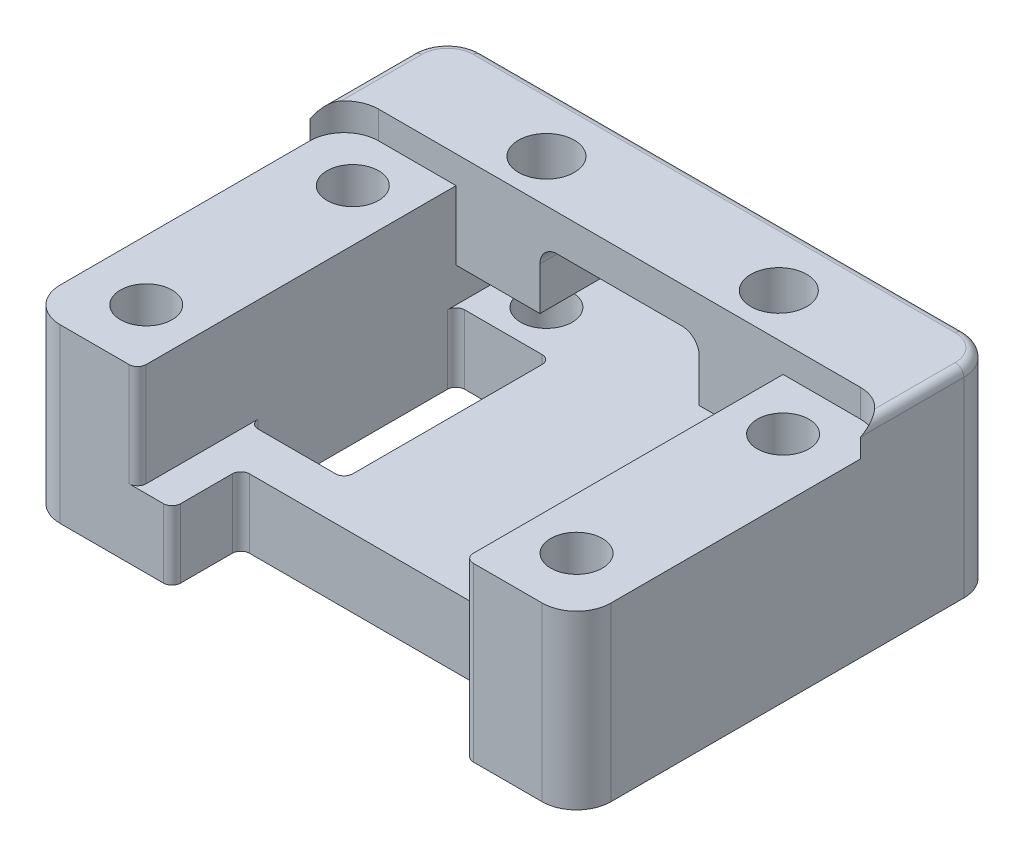
SolidWorks part; units mm, degrees
material "PET"
ref_plane "Front Plane" through (0, 0, 0) normal (0, 0, 1) x (1, 0, 0)
ref_plane "Top Plane" through (0, 0, 0) normal (0, 1, 0) x (1, 0, 0)
ref_plane "Right Plane" through (0, 0, 0) normal (1, 0, 0) x (0, 0, -1)
sketch "Sketch1" plane through (0, 0, 0) normal (0, 1, 0) x (1, 0, 0)
  line L1 (-16, 12.25) -> (16, 12.25)
  line L2 (-16, 12.25) -> (-16, -12.25)
  line L3 (-16, -12.25) -> (16, -12.25)
  line L4 (16, 12.25) -> (16, -12.25)
  line L5 (-16, 12.25) -> (16, -12.25) construction
  line L6 (-16, -12.25) -> (16, 12.25) construction
  point P0 (0, 0)
  dimension "D1" = 32
  dimension "D2" = 24.5
extrude "Boss-Extrude1" add sketch "Sketch1" along normal blind 10
sketch "Sketch2" plane through (0, 10, 0) normal (0, 1, 0) x (1, 0, 0)
  line L0 (-16, -12.25) -> (16, -12.25) construction
  line L1 (-9.5, 12.25) -> (9.5, 12.25)
  line L2 (-9.5, 12.25) -> (-9.5, -12.25)
  line L3 (-9.5, -12.25) -> (9.5, -12.25)
  line L4 (9.5, 12.25) -> (9.5, -12.25)
  line L5 (-9.5, 12.25) -> (9.5, -12.25) construction
  line L6 (-9.5, -12.25) -> (9.5, 12.25) construction
  point P0 (0, 0)
  dimension "D1" = 19
extrude "Cut-Extrude1" cut sketch "Sketch2" against normal blind 6
sketch "Sketch12" plane through (0, 10, 0) normal (0, 1, 0) x (1, 0, 0)
  line L0 (16, -12.25) -> (16, 12.25) construction
  line L1 (-16, 12.25) -> (16, 12.25)
  line L2 (-16, 12.25) -> (-16, 6.25)
  line L3 (-16, 6.25) -> (16, 6.25)
  line L4 (16, 12.25) -> (16, 6.25)
  dimension "D1" = 6
extrude "Boss-Extrude2" add sketch "Sketch12" against normal offset from surface (5.6 mm away) 2 from offset 1.6
sketch "Sketch13" plane through (0, 0, -12.25) normal (0, 0, -1) x (-1, 0, 0)
  line L0 (0, 6) -> (0, 11.6) construction
  line L1 (9.5, 6) -> (-9.5, 6) construction
  line L2 (-16, 11.6) -> (16, 11.6) construction
  line L4 (-4.625, 9.5) -> (4.625, 9.5)
  line L5 (-4.625, 9.5) -> (-4.625, 6)
  line L6 (-4.625, 6) -> (4.625, 6)
  line L7 (4.625, 9.5) -> (4.625, 6)
  line L8 (-4.625, 9.5) -> (4.625, 6) construction
  line L9 (-4.625, 6) -> (4.625, 9.5) construction
  point P6 (0, 7.75)
  dimension "D1" = 3.5
  dimension "D2" = 9.25
extrude "Cut-Extrude7" cut sketch "Sketch13" against normal through all
sketch "Sketch9" plane through (0, 4, 0) normal (0, 1, 0) x (1, 0, 0)
  line L0 (9.5, 8.75) -> (-9.5, 8.75) construction
  line L1 (9.5, -12.25) -> (9.5, 12.25) construction
  line L2 (-9.5, 12.25) -> (-9.5, -12.25) construction
  line L3 (0, 12.25) -> (0, -12.25) construction
  line L4 (9.5, 12.25) -> (-9.5, 12.25) construction
  line L5 (-9.5, -12.25) -> (9.5, -12.25) construction
  circle A0 centre (-6.75, 8.75) radius 1.5
  circle A1 centre (6.75, 8.75) radius 1.5
  dimension "D1" = 3
  dimension "D2" = 13.5
  dimension "D3" = 3.5
extrude "Cut-Extrude5" cut sketch "Sketch9" against normal through all both and the other way through all
sketch "Sketch3" plane through (0, 10, 0) normal (0, 1, 0) x (1, 0, 0)
  line L0 (-9.5, 12.25) -> (-16, 12.25) construction
  line L1 (-12.5, 8.75) -> (-12.5, -9.5) construction
  line L2 (-16, -12.25) -> (-9.5, -12.25) construction
  line L3 (12.5, 8.75) -> (12.5, -9.5) construction
  line L4 (-12.5, 8.75) -> (12.5, 8.75) construction
  line L5 (0, 12.25) -> (0, -12.3398) construction
  line L6 (-12.5, 3.25) -> (12.5, 3.25) construction
  line L7 (-12.5, -8.75) -> (12.5, -8.75) construction
  line L8 (-9.5, -12.25) -> (9.5, -12.25) construction
  line L9 (9.5, 12.25) -> (-9.5, 12.25) construction
  line L10 (-16, 6.25) -> (-16, -12.25) construction
  line L11 (16, -12.25) -> (16, 6.25) construction
  circle A1 centre (-12.5, 3.25) radius 1.5
  circle A2 centre (-12.5, -8.75) radius 1.5
  circle A3 centre (12.5, -8.75) radius 1.5
  circle A4 centre (12.5, 3.25) radius 1.5
  circle A5 centre (-6.75, 8.75) radius 1.5
  circle A6 centre (6.75, 8.75) radius 1.5
  dimension "D1" = 3
  dimension "D2" = 9
  dimension "D3" = 3.5
  dimension "D4" = 3.5
  dimension "D5" = 3.5
  dimension "D6" = 3.5
  dimension "D7" = 13.5
extrude "Cut-Extrude2" cut sketch "Sketch3" against normal blind 4
sketch "Sketch4" plane through (0, 6, 0) normal (0, 1, 0) x (1, 0, 0)
  circle A0 centre (-12.5, 3.25) radius 1.5
  circle A1 centre (-12.5, -8.75) radius 1.5
  circle A2 centre (12.5, 3.25) radius 1.5
  circle A3 centre (12.5, -8.75) radius 1.5
  dimension "D1" = 3
extrude "Cut-Extrude3" cut sketch "Sketch4" against normal through all
sketch "Sketch10" plane through (0, 4, 0) normal (0, 1, 0) x (1, 0, 0)
  circle A0 centre (-6.75, 8.75) radius 1.5
  circle A1 centre (6.75, 8.75) radius 1.5
  dimension "D1" = 3
extrude "Cut-Extrude6" [suppressed] cut sketch "Sketch10" against normal through all
sketch "Sketch6" plane through (0, 4, 0) normal (0, 1, 0) x (1, 0, 0)
  line L0 (9.5, -12.25) -> (9.5, 12.25) construction
  line L1 (-9.5, 6.25) -> (-4, 6.25)
  line L2 (-9.5, 6.25) -> (-9.5, -5.75)
  line L3 (-9.5, -5.75) -> (-4, -5.75)
  line L4 (-4, 6.25) -> (-4, -5.75)
  line L5 (9.5, -8.25) -> (-7.5, -8.25)
  line L6 (9.5, -8.25) -> (9.5, -12.25)
  line L7 (9.5, -12.25) -> (-7.5, -12.25)
  line L8 (-7.5, -8.25) -> (-7.5, -12.25)
  line L9 (-9.5, -12.25) -> (9.5, -12.25) construction
  line L10 (9.5, 12.25) -> (-9.5, 12.25) construction
  line L13 (-9.5, 12.25) -> (-9.5, -12.25) construction
  dimension "D1" = 5.5
  dimension "D2" = 6
  dimension "D3" = 17
  dimension "D4" = 4
  dimension "D5" = 12
extrude "Cut-Extrude4" cut sketch "Sketch6" against normal through all and the other way through all
sketch "Sketch16" plane through (0, 10, 0) normal (0, 1, 0) x (1, 0, 0)
  line L1 (-16, 6.25) -> (-14, 6.25)
  line L2 (-16, 6.25) -> (-16, 4.25)
  line L3 (-16, 4.25) -> (-14, 4.25)
  line L4 (-14, 6.25) -> (-14, 4.25)
  line L5 (16, 6.25) -> (14, 6.25)
  line L6 (16, 6.25) -> (16, 4.25)
  line L7 (16, 4.25) -> (14, 4.25)
  line L8 (14, 6.25) -> (14, 4.25)
  dimension "D1" = 2
  dimension "D2" = 2
extrude "Boss-Extrude3" add sketch "Sketch16" along normal up to surface (1.6 mm away) up to face at (-6.75, 11.6, -7.25)
sketch "Sketch17" plane through (0, 11.6, 0) normal (0, 1, 0) x (1, 0, 0)
  circle A0 centre (-14, 4.25) radius 2
  circle A1 centre (14, 4.25) radius 2
extrude "Cut-Extrude10" cut sketch "Sketch17" against normal up to surface (1.6 mm away) up to face at (-12.5, 10, 10.25)
fillet "Fillet1" radius 2 4 edges at (-16, 5.8, -12.25) (-16, 5, 12.25) (16, 5.8, -12.25) (16, 5, 12.25)
fillet "Fillet3" radius 0.5 9 edges at (-4, 2, 5.75) (-4, 2, -6.25) (-9.5, 2, -6.25) (-9.5, 2, 5.75) (9.5, 5, 12.25) (9.5, 2, 8.25) (-7.5, 2, 8.25) (-9.5, 7, 12.25) (-7.5, 2, 12.25)
fillet "Fillet4" radius 0.5 5 edges at (16, 11.6, -7.25) (15.4142, 11.6, -11.6642) (0, 11.6, -12.25) (-15.4142, 11.6, -11.6642) (-16, 11.6, -7.25)
fillet "Fillet5" radius 1 2 edges at (-4.625, 9.5, -9.25) (4.625, 9.5, -9.25)
sketch "Sketch14" plane through (0, 11.6, 0) normal (0, 1, 0) x (1, 0, 0)
  circle A0 centre (6.75, 8.75) radius 1.625
  circle A1 centre (-6.75, 8.75) radius 1.625
  dimension "D1" = 3.25
extrude "Cut-Extrude8" cut sketch "Sketch14" against normal up to surface (5.6 mm away) up to face at (6.75, 6, -7.25)
